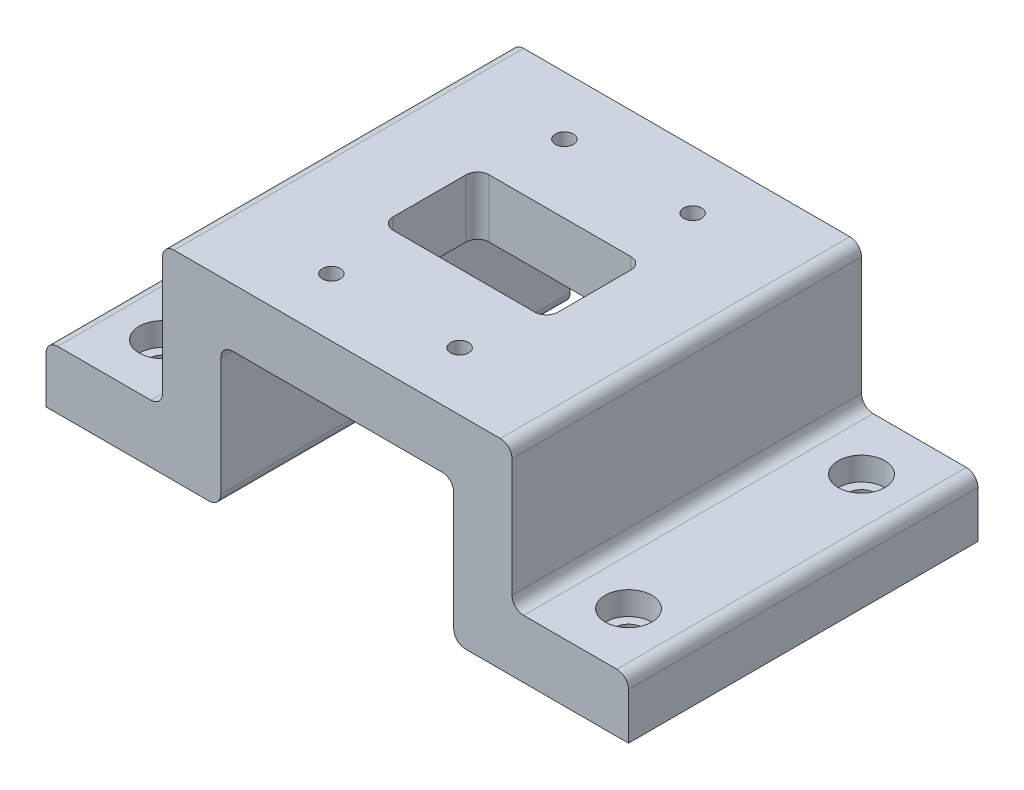
SolidWorks part; units mm, degrees
ref_plane "Front Plane" through (0, 0, 0) normal (0, 0, 1) x (1, 0, 0)
ref_plane "Top Plane" through (0, 0, 0) normal (0, 1, 0) x (1, 0, 0)
ref_plane "Right Plane" through (0, 0, 0) normal (1, 0, 0) x (0, 0, -1)
sketch "Sketch2" plane through (0, 0, 0) normal (0, 1, 0) x (1, 0, 0)
  line L0 (-30, 30) -> (30, 30)
  line L1 (-30, 30) -> (-30, -30)
  line L2 (30, 30) -> (30, -30)
  line L3 (-30, -30) -> (30, -30)
  line L4 (30, -30) -> (-30, 30) construction
  point P0 (0, 0)
  dimension "D1" = 60
  dimension "D2" = 60
extrude "Boss-Extrude1" add sketch "Sketch2" along normal blind 10
sketch "Sketch7" plane through (0, 10, 0) normal (0, 1, 0) x (1, 0, 0)
  line L0 (-14.16, 8.25) -> (14.16, 8.25)
  line L1 (-14.16, 8.25) -> (-14.16, -8.25)
  line L2 (14.16, 8.25) -> (14.16, -8.25)
  line L3 (-14.16, -8.25) -> (14.16, -8.25)
  line L4 (14.16, -8.25) -> (-14.16, 8.25) construction
  point P0 (0, 0)
  dimension "D1" = 28.32
  dimension "D2" = 16.5
extrude "Cut-Extrude2" cut sketch "Sketch7" against normal through all
fillet "Fillet2" radius 2 4 edges at (-14.16, 5, 8.25) (14.16, 5, 8.25) (14.16, 5, -8.25) (-14.16, 5, -8.25)
hole_wizard "CBORE for M2.5 SHCS2" positions "Sketch9" profile "Sketch10" counterbore size "M2.5" standard "ANSI Metric" end condition up to next
sketch "Sketch9" plane through (0, 0, 0) normal (0, -1, 0) x (-1, 0, 0)
  line L0 (-11, 20) -> (11, 20) construction
  line L1 (-11, 20) -> (-11, -20) construction
  line L2 (11, 20) -> (11, -20) construction
  line L3 (-11, -20) -> (11, -20) construction
  line L4 (11, -20) -> (-11, 20) construction
  point P0 (11, -20)
  point P2 (-11, -20)
  point P4 (11, 20)
  point P6 (-11, 20)
  point P50 (0, 0)
  dimension "D1" = 22
  dimension "D2" = 40
sketch "Sketch10" plane through (-11, 0, 20) normal (1, 0, 0) x (0, 0, -1)
  line L0 (0, 0) -> (0, 10)
  line L1 (0, 10) -> (1.55, 10)
  line L3 (1.55, 10) -> (1.55, 2.5)
  line L4 (1.55, 2.5) -> (2.75, 2.5)
  line L5 (2.75, 2.5) -> (2.75, 0)
  line L7 (2.75, 0) -> (0, 0)
  line L11 (0, -6.35) -> (0, 107.95) construction
  dimension "Thru Hole Dia." = 3.1
  dimension "Thru Hole Depth" = 10
  dimension "C'Bore Dia." = 5.5
  dimension "C'Bore Depth" = 2.5
other "Move Face1" face at (11, 2.5, 18.45) face at (-11, 2.5, 18.45) face at (11, 2.5, -21.55) face at (-11, 2.5, -21.55) parameters "D1"=3.5
sketch "Sketch11" plane through (0, 0, -30) normal (0, 0, -1) x (-1, 0, 0)
  line L0 (-30, 0) -> (-20, 0)
  line L1 (-30, 0) -> (-30, -24.3)
  line L2 (-20, 0) -> (-20, -24.3)
  line L3 (-30, -24.3) -> (-20, -24.3)
  line L4 (-30, 0) -> (30, 0) construction
  line L5 (-30, 10) -> (30, 10) construction
  dimension "D1" = 10
  dimension "D2" = 34.3
extrude "Boss-Extrude2" add sketch "Sketch11" against normal up to surface (60 mm away) up to face at (0, 5, 30)
sketch "Sketch12" plane through (0, -24.3, 0) normal (0, -1, 0) x (1, 0, 0)
  line L0 (30, 30) -> (30, -30)
  line L1 (30, 30) -> (50, 30)
  line L2 (30, -30) -> (50, -30)
  line L3 (50, 30) -> (50, -30)
  dimension "D1" = 20
extrude "Boss-Extrude3" add sketch "Sketch12" against normal blind 10
hole_wizard "CBORE for M4 SHCS1" positions "Sketch13" profile "Sketch14" counterbore size "M4" standard "ANSI Metric" end condition up to next
sketch "Sketch13" plane through (0, -14.3, 0) normal (0, 1, 0) x (1, 0, 0)
  line L4 (40, 0) -> (50, 0) construction
  line L5 (50, 30) -> (50, -30) construction
  line L7 (40, 20) -> (40, -20) construction
  line L9 (50, -30) -> (30, -30) construction
  point P0 (40, 20)
  point P2 (40, -20)
  point P24 (40, 0)
  point P28 (40, -30)
  dimension "D1" = 40
sketch "Sketch14" plane through (40, -14.3, -20) normal (1, 0, 0) x (0, 0, 1)
  line L0 (0, 0) -> (0, 10.001)
  line L1 (0, 10.001) -> (2.4, 10.001)
  line L3 (2.4, 10.001) -> (2.4, 4)
  line L4 (2.4, 4) -> (4, 4)
  line L5 (4, 4) -> (4, 0)
  line L7 (4, 0) -> (0, 0)
  line L11 (0, -6.35) -> (0, 107.95) construction
  dimension "Thru Hole Dia." = 4.8
  dimension "Thru Hole Depth" = 10.001
  dimension "C'Bore Dia." = 8
  dimension "C'Bore Depth" = 4
mirror "Mirror1" about plane through (0, 0, 0) normal (1, 0, 0) of "CBORE for M4 SHCS1", "Boss-Extrude3", "Boss-Extrude2"
fillet "Fillet5" radius 2 10 edges at (30, 10, 0) (-30, 10, 0) (-20, -24.3, 0) (20, -24.3, 0) (20, 0, 0) (-20, 0, 0) (30, -14.3, 0) (-30, -14.3, 0) (-50, -14.3, 0) (50, -14.3, 0)
